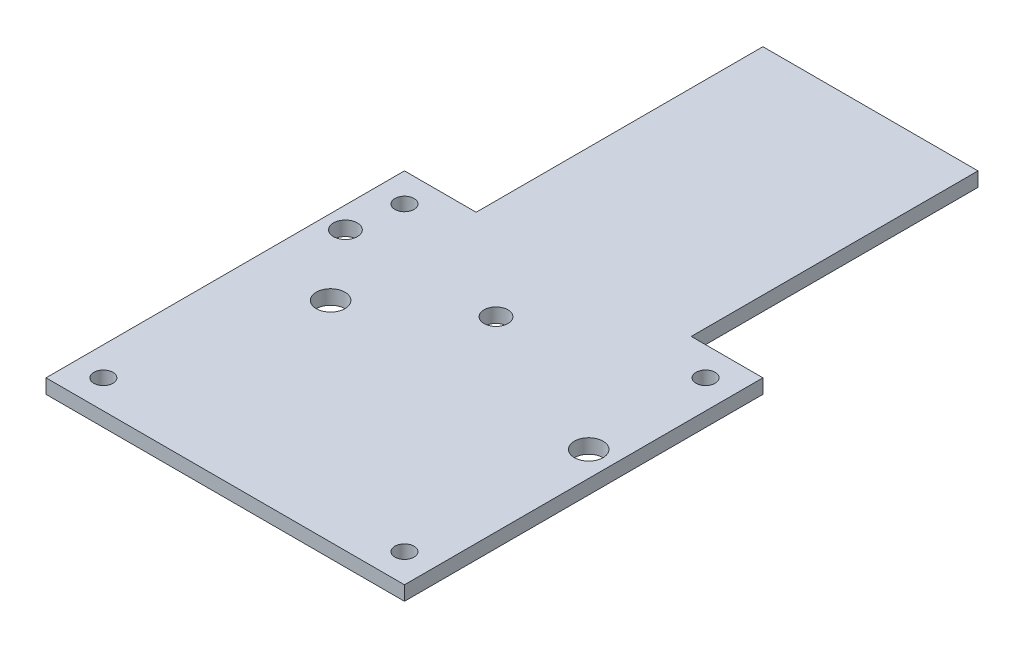
SolidWorks part; units mm, degrees
material "5052-H32"
ref_plane "Front Plane" through (0, 0, 0) normal (0, 0, 1) x (1, 0, 0)
ref_plane "Top Plane" through (0, 0, 0) normal (0, 1, 0) x (1, 0, 0)
ref_plane "Right Plane" through (0, 0, 0) normal (1, 0, 0) x (0, 0, -1)
sketch "Sketch1" plane through (0, 0, 0) normal (0, 1, 0) x (1, 0, 0)
  line L0 (22.5, 37.5) -> (37.5, 37.5)
  line L1 (-37.5, -37.5) -> (37.5, -37.5)
  line L2 (-37.5, -37.5) -> (-37.5, 37.5)
  line L3 (-37.5, 37.5) -> (-22.5, 37.5)
  line L4 (37.5, -37.5) -> (37.5, 37.5)
  line L5 (-37.5, -37.5) -> (37.5, 37.5) construction
  line L6 (-37.5, 37.5) -> (37.5, -37.5) construction
  line L7 (-22.5, 97.5) -> (22.5, 97.5)
  line L8 (-22.5, 97.5) -> (-22.5, 37.5)
  line L10 (22.5, 97.5) -> (22.5, 37.5)
  line L11 (-22.5, 97.5) -> (22.5, 37.5) construction
  line L12 (-22.5, 37.5) -> (22.5, 97.5) construction
  circle A0 centre (31.5, 31.5) radius 2
  circle A1 centre (31.5, -31.5) radius 2
  circle A2 centre (-31.5, -31.5) radius 2
  circle A3 centre (-31.5, 31.5) radius 2
  circle A4 centre (32.25, 6.3) radius 3
  circle A5 centre (-21.75, 6.3) radius 3
  circle A6 centre (-33, 20.65) radius 2.5
  circle A7 centre (-1.5, 20.65) radius 2.5
  point P0 (0, 0)
  point P8 (0, 67.5)
  point P17 (0, 0)
  dimension "D4" = 4
  dimension "D9" = 5
  dimension "D10" = 6
  dimension "D1" = 75
  dimension "D2" = 75
  dimension "D3" = 6
  dimension "D6" = 45
  dimension "D7" = 60
  dimension "D8" = 0
  dimension "D5" = 4
extrude "Boss-Extrude1" add sketch "Sketch1" along normal blind 3
